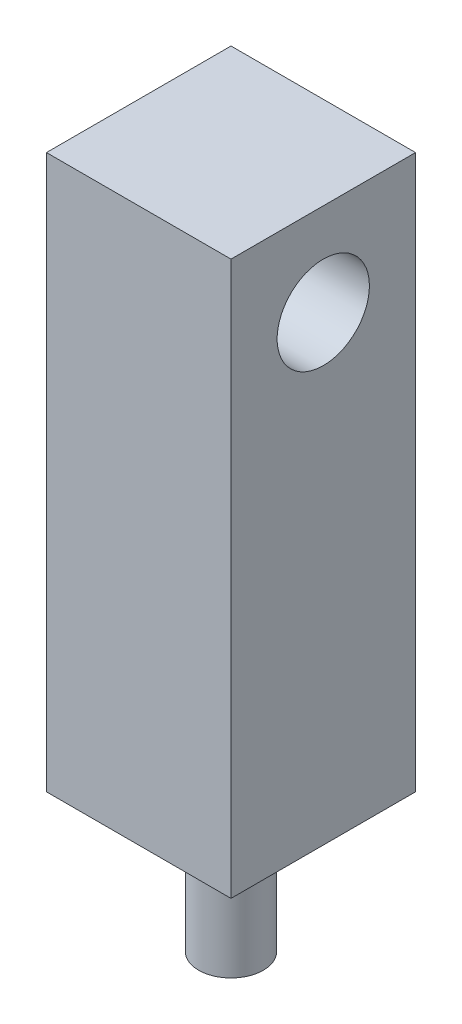
SolidWorks part; units mm, degrees
ref_plane "Front Plane" through (0, 0, 0) normal (0, 0, 1) x (1, 0, 0)
ref_plane "Top Plane" through (0, 0, 0) normal (0, 1, 0) x (1, 0, 0)
ref_plane "Right Plane" through (0, 0, 0) normal (1, 0, 0) x (0, 0, -1)
sketch "Sketch2" plane through (0, 0, 0) normal (0, 1, 0) x (1, 0, 0)
  line L1 (-2, 2) -> (2, 2)
  line L2 (-2, 2) -> (-2, -2)
  line L3 (-2, -2) -> (2, -2)
  line L4 (2, 2) -> (2, -2)
  line L5 (-2, 2) -> (2, -2) construction
  line L6 (-2, -2) -> (2, 2) construction
  point P0 (0, 0)
extrude "Boss-Extrude1" add sketch "Sketch2" along normal blind 12
sketch "Sketch3" plane through (0, 0, 0) normal (0, 1, 0) x (1, 0, 0)
  circle A0 centre (0, 0) radius 0.7
extrude "Boss-Extrude2" add sketch "Sketch3" against normal blind 3
ref_plane "Plane1" through (2, 0, 0) normal (1, 0, 0) x (0, 0, -1)
sketch "Sketch4" plane through (2, 0, 0) normal (1, 0, 0) x (0, 0, -1)
  line L0 (0, 0) -> (0, 10) construction
  line L1 (-2, 0) -> (2, 0) construction
  circle A0 centre (0, 10) radius 1
extrude "Cut-Extrude1" cut sketch "Sketch4" against normal blind 3
